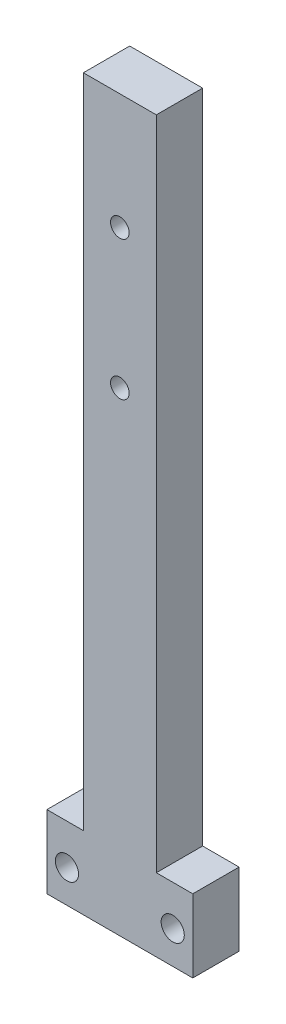
SolidWorks part; units mm, degrees
ref_plane "Front Plane" through (0, 0, 0) normal (0, 0, 1) x (1, 0, 0)
ref_plane "Top Plane" through (0, 0, 0) normal (0, 1, 0) x (1, 0, 0)
ref_plane "Right Plane" through (0, 0, 0) normal (1, 0, 0) x (0, 0, -1)
sketch "Sketch1" plane through (0, 0, 0) normal (0, 0, 1) x (1, 0, 0)
  line L0 (-20, 0) -> (20, 0)
  line L1 (20, 0) -> (20, 20)
  line L2 (20, 20) -> (10, 20)
  line L3 (10, 20) -> (10, 200)
  line L4 (10, 200) -> (-10, 200)
  line L5 (-10, 200) -> (-10, 20)
  line L6 (-10, 20) -> (-20, 20)
  line L7 (-20, 20) -> (-20, 0)
  line L8 (0, 0) -> (0, 200) construction
  dimension "D1" = 40
  dimension "D2" = 20
  dimension "D3" = 20
  dimension "D4" = 180
extrude "Boss-Extrude1" add sketch "Sketch1" along normal blind 12.7
hole_wizard "1/4-20 Tapped Hole1" positions "Sketch2" profile "Sketch3" tap size "1/4-20" standard "ANSI Inch" end condition through all
sketch "Sketch2" plane through (0, 0, 0) normal (0, 0, -1) x (-1, 0, 0)
  circle A0 centre (0, 130.15) radius 3.2639 construction
  circle A1 centre (0, 168.25) radius 3.2639 construction
  point P0 (0, 168.25)
  point P2 (0, 130.15)
  point P5 (0, 0)
  point P6 (0, 0)
  point P9 (0, 0)
sketch "Sketch3" plane through (0, 168.25, 0) normal (1, 0, 0) x (0, 1, 0)
  line L0 (0, 0) -> (0, 12.7)
  line L1 (0, 12.7) -> (2.5527, 12.7)
  line L2 (2.5527, 12.7) -> (2.5527, 1.055)
  line L3 (2.5527, 1.055) -> (3.81, 0)
  line L5 (3.81, 0) -> (0, 0)
  line L6 (-2.5527, 1.055) -> (-3.81, 0) construction
  line L11 (0, -6.35) -> (0, 107.95) construction
  dimension "Thru Tap Drill Dia." = 5.1054
  dimension "Thru Tap Drill Depth" = 12.7
  dimension "Near C'Sink Dia." = 7.62
  dimension "Near C'Sink Angle" = 100
cosmetic thread "Hole Thread1"
cosmetic thread "Hole Thread2"
hole_wizard "1/4 (0.25) Diameter Hole1" positions "Sketch4" profile "Sketch6" hole size "1/4" standard "ANSI Inch"
sketch "Sketch4" plane through (0, 0, 0) normal (0, 0, -1) x (-1, 0, 0)
  circle A0 centre (-14.5, 9) radius 2.5527 construction
  circle A1 centre (14.5, 9) radius 2.5527 construction
  point P0 (14.5, 9)
  point P2 (-14.5, 9)
  point P5 (0, 0)
  point P8 (0, 0)
sketch "Sketch6" plane through (-14.5, 9, 0) normal (1, 0, 0) x (0, 1, 0)
  line L0 (0, 0) -> (0, 20.9577)
  line L1 (0, 20.9577) -> (3.175, 19.05)
  line L2 (3.175, 19.05) -> (3.175, 0)
  line L5 (3.175, 0) -> (0, 0)
  line L10 (0, 20.9577) -> (-3.175, 19.05) construction
  line L11 (0, -6.35) -> (0, 107.95) construction
  dimension "Hole Dia." = 6.35
  dimension "Hole Depth" = 19.05
  dimension "Drill Angle" = 118
